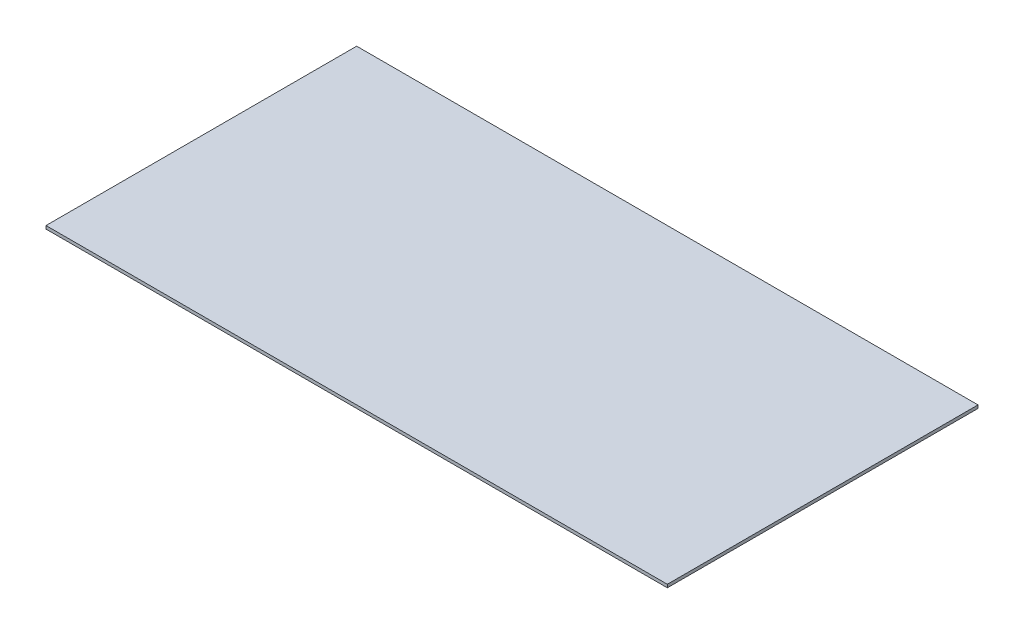
SolidWorks part; units mm, degrees
ref_plane "Front" through (0, 0, 0) normal (0, 0, 1) x (1, 0, 0)
ref_plane "Top" through (0, 0, 0) normal (0, 1, 0) x (1, 0, 0)
ref_plane "Right" through (0, 0, 0) normal (1, 0, 0) x (0, 0, -1)
sketch "Croquis1" plane through (0, 0, 0) normal (0, 1, 0) x (1, 0, 0)
  line L1 (-1000, 500) -> (1000, 500)
  line L2 (-1000, 500) -> (-1000, -500)
  line L3 (-1000, -500) -> (1000, -500)
  line L4 (1000, 500) -> (1000, -500)
  line L5 (-1000, 500) -> (1000, -500) construction
  line L6 (-1000, -500) -> (1000, 500) construction
  point P0 (0, 0)
  dimension "D1" = 2000
  dimension "D2" = 1000
extrude "Saliente-Extruir1" add sketch "Croquis1" along normal blind 10
